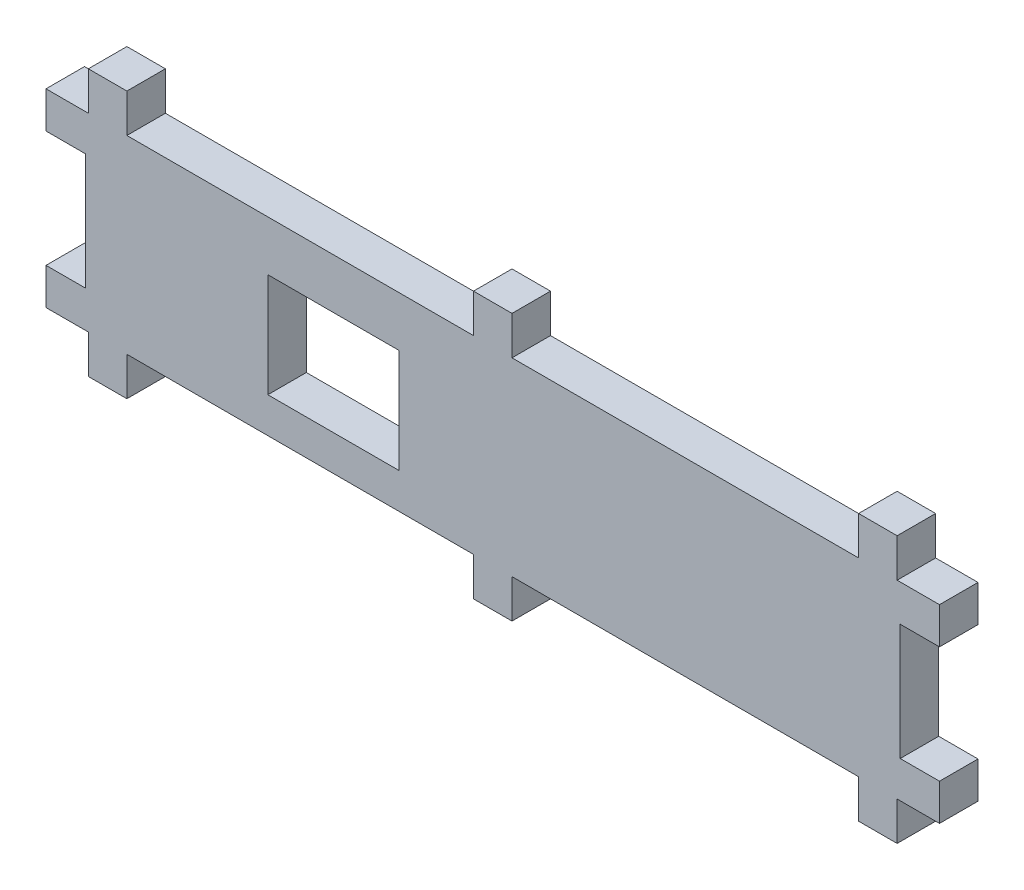
SolidWorks part; units mm, degrees
ref_plane "Front" through (0, 0, 0) normal (0, 0, 1) x (1, 0, 0)
ref_plane "Top" through (0, 0, 0) normal (0, 1, 0) x (1, 0, 0)
ref_plane "Right" through (0, 0, 0) normal (1, 0, 0) x (0, 0, -1)
sketch "Sketch1" plane through (0, 0, 0) normal (0, 0, 1) x (1, 0, 0)
  line L1 (-58, -6.15) -> (58, -6.15)
  line L2 (-58, -6.15) -> (-58, 6.15)
  line L3 (-58, 6.15) -> (58, 6.15)
  line L4 (58, -6.15) -> (58, 6.15)
  line L5 (-58, -6.15) -> (58, 6.15) construction
  line L6 (-58, 6.15) -> (58, -6.15) construction
  point P0 (0, 0)
  dimension "D1" = 12.3
  dimension "D2" = 116
extrude "Boss-Extrude1" add sketch "Sketch1" along normal blind 5
sketch "Sketch2" plane through (0, -6.15, 0) normal (0, -1, 0) x (1, 0, 0)
  line L0 (-58, 5) -> (58, 5) construction
  line L1 (-52.5, 5) -> (-47.5, 5)
  line L2 (-52.5, 5) -> (-52.5, 0)
  line L3 (-52.5, 0) -> (-47.5, 0)
  line L4 (-47.5, 5) -> (-47.5, 0)
  line L5 (-58, 0) -> (58, 0) construction
  line L6 (-58, 5) -> (-58, 0) construction
  line L7 (-2.5, 5) -> (2.5, 5)
  line L8 (-2.5, 5) -> (-2.5, 0)
  line L9 (-2.5, 0) -> (2.5, 0)
  line L10 (2.5, 5) -> (2.5, 0)
  line L11 (47.5, 5) -> (52.5, 5)
  line L12 (47.5, 5) -> (47.5, 0)
  line L13 (47.5, 0) -> (52.5, 0)
  line L14 (52.5, 5) -> (52.5, 0)
  point P16 (-58, 2.5)
  dimension "D1" = 5
  dimension "D2" = 5
  dimension "D3" = 5
  dimension "D4" = 45
  dimension "D5" = 95
  dimension "D6" = 5.5
extrude "Boss-Extrude2" add sketch "Sketch2" along normal blind 5
mirror "Mirror1" about plane through (-58, 6.15, 5) normal (0, -1, 0) of bodies 102
sketch "Sketch3" plane through (0, 0, 5) normal (0, 0, 1) x (1, 0, 0)
  line L0 (-58, 18.45) -> (-58, -6.15) construction
  line L1 (-29.2, -1.55) -> (-12.2, -1.55)
  line L2 (-29.2, -1.55) -> (-29.2, 11.95)
  line L3 (-29.2, 11.95) -> (-12.2, 11.95)
  line L4 (-12.2, -1.55) -> (-12.2, 11.95)
  line L5 (-47.5, -6.15) -> (-2.5, -6.15) construction
  dimension "D1" = 28.8
  dimension "D2" = 17
  dimension "D3" = 4.6
  dimension "D4" = 13.5
extrude "Cut-Extrude1" cut sketch "Sketch3" against normal through all
sketch "Sketch4" plane through (-58, 0, 0) normal (-1, 0, 0) x (0, 0, 1)
  line L0 (0, 18.45) -> (0, -6.15) construction
  line L1 (0, 13.7) -> (5, 13.7)
  line L2 (0, 13.7) -> (0, -1.4)
  line L3 (0, -1.4) -> (5, -1.4)
  line L4 (5, 13.7) -> (5, -1.4)
  line L5 (5, 18.45) -> (5, -6.15) construction
  line L6 (5, 23.45) -> (0, 23.45) construction
  dimension "D1" = 15.1
  dimension "D2" = 9.75
extrude "Cut-Extrude2" cut sketch "Sketch4" against normal blind 5.1
mirror "Mirror2" about plane through (0, 0, 0) normal (1, 0, 0) of "Cut-Extrude2"
